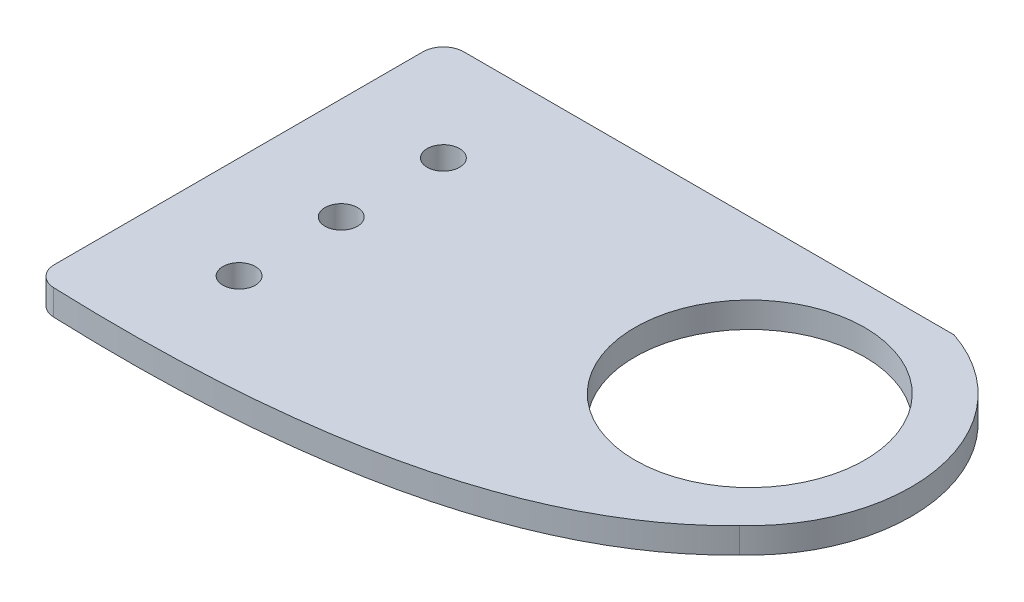
SolidWorks part; units mm, degrees
ref_plane "Front Plane" through (0, 0, 0) normal (0, 0, 1) x (1, 0, 0)
ref_plane "Top Plane" through (0, 0, 0) normal (0, 1, 0) x (1, 0, 0)
ref_plane "Right Plane" through (0, 0, 0) normal (1, 0, 0) x (0, 0, -1)
sketch "Sketch1" plane through (0, 0, 0) normal (0, 1, 0) x (1, 0, 0)
  line L0 (-52.3418, 21.4668) -> (-52.3418, -29.3332)
  line L1 (-52.3418, -29.3332) -> (-8.3234, -29.3332) construction
  line L2 (-8.3234, -29.3332) -> (-8.3234, 8.0464) construction
  line L3 (11.1582, 21.4668) -> (-52.3418, 21.4668)
  line L4 (-52.3418, -29.3332) -> (0, -31.75) construction
  line L5 (0, -31.75) -> (18.3464, -12.4137) construction
  circle A0 centre (4.8082, 2.4168) radius 14.2875
  circle A1 centre (-39.6418, 8.7668) radius 2.0193
  circle A2 centre (-39.6418, -3.9332) radius 2.0193
  circle A3 centre (-39.6418, -16.6332) radius 2.0193
  arc A4 (11.1582, 21.4668) -> (-8.3234, -12.7748) centre (4.8082, 2.4168) cw
  spline S0 degree 2 poles (-52.3418, -29.3332) (0, -31.75) (18.3464, -12.4137) knots 0 0 0 1 1 1
  point P15 (0, 0)
  dimension "D1" = 28.575
  dimension "D2" = 4.0386
  dimension "D3" = 44.45
  dimension "D4" = 6.35
  dimension "D6" = 63.5
  dimension "D7" = 12.7
  dimension "D8" = 50.8
  dimension "D9" = 19.05
  dimension "D5" = 3
extrude "Boss-Extrude1" add sketch "Sketch1" along normal blind 3.175
fillet "Fillet1" radius 2.54 2 edges at (-52.3418, 1.5875, -21.4668) (-52.3418, 1.5875, 29.3332)
